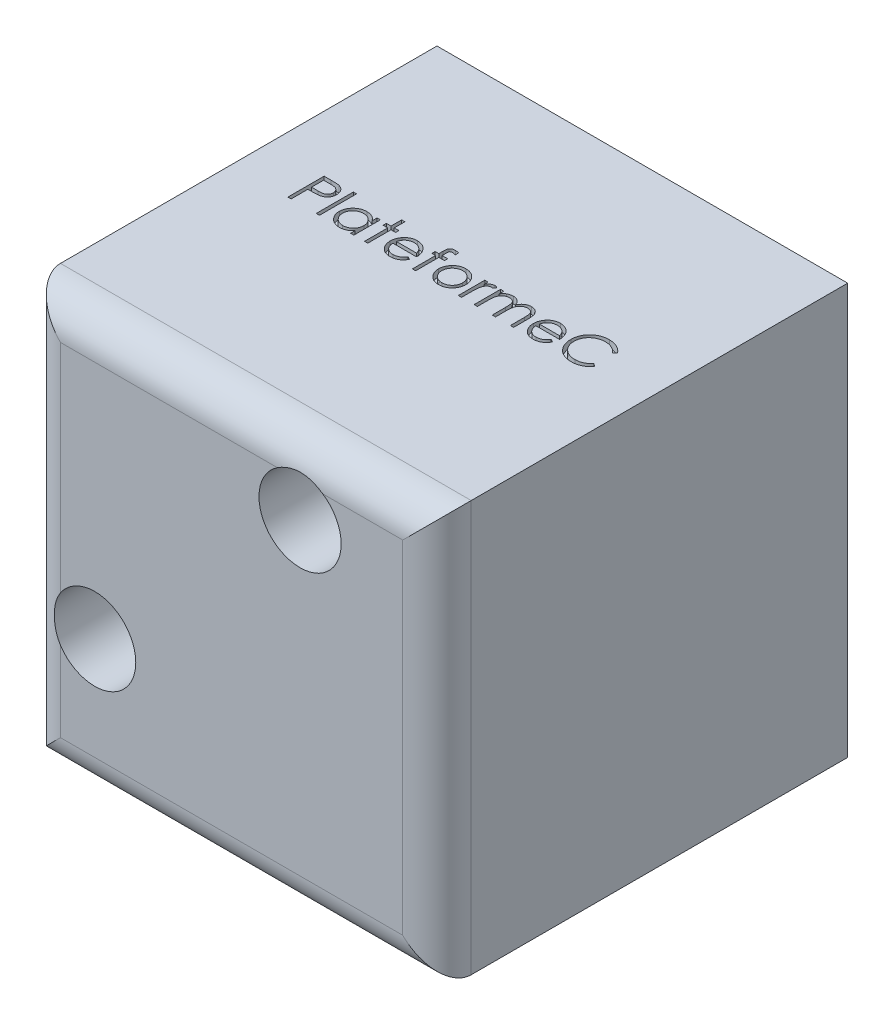
SolidWorks part; units mm, degrees
ref_plane "Plan de face" through (0, 0, 0) normal (0, 0, 1) x (1, 0, 0)
ref_plane "Plan de dessus" through (0, 0, 0) normal (0, 1, 0) x (1, 0, 0)
ref_plane "Plan de droite" through (0, 0, 0) normal (1, 0, 0) x (0, 0, -1)
sketch "Esquisse1" plane through (0, 0, 0) normal (0, 0, 1) x (1, 0, 0)
  line L1 (0, 0) -> (-60, 0)
  line L2 (0, 0) -> (0, 60)
  line L3 (0, 60) -> (-60, 60)
  line L4 (-60, 0) -> (-60, 60)
  dimension "D1" = 60
  dimension "D2" = 60
extrude "Boss.-Extru.1" add sketch "Esquisse1" along normal blind 60
sketch "Esquisse3" plane through (0, 0, 0) normal (0, 0, -1) x (-1, 0, 0)
  line L0 (60, 60) -> (60, 20)
  line L1 (60, 60) -> (60, 0) construction
  line L2 (60, 20) -> (58, 20)
  line L3 (58, 20) -> (58, 58)
  line L4 (58, 58) -> (20, 58)
  line L5 (20, 58) -> (20, 60)
  line L6 (0, 60) -> (60, 60) construction
  line L7 (20, 60) -> (60, 60)
  dimension "D1" = 40
  dimension "D2" = 40
  dimension "D3" = 2
  dimension "D4" = 2
extrude "Boss.-Extru.3" add sketch "Esquisse3" along normal blind 40
sketch "Esquisse6" plane through (-60, 0, 0) normal (-1, 0, 0) x (0, 0, 1)
  line L0 (30, 0) -> (30, 60) construction
  line L1 (60, 0) -> (0, 0) construction
  line L2 (60, 60) -> (-40, 60) construction
  text T0 "PING" font "Century Gothic" height in points 48
extrude "Enlèv. mat.-Extru.3" cut sketch "Esquisse6" against normal blind 1
sketch "Esquisse7" plane through (0, 60, 0) normal (0, 1, 0) x (1, 0, 0)
  line L0 (0, -30) -> (-60, -30) construction
  line L1 (0, -60) -> (0, 0) construction
  line L2 (-60, -60) -> (-60, 40) construction
  text T0 "PlateformeC" font "Century Gothic" height in points 20
extrude "Enlèv. mat.-Extru.4" cut sketch "Esquisse7" against normal blind 1
sketch "Esquisse8" plane through (-60, 0, 0) normal (-1, 0, 0) x (0, 0, 1)
  line L0 (-40, 20) -> (0, 60)
  line L1 (60, 60) -> (-40, 60) construction
  line L2 (0, 60) -> (-40, 60)
  line L3 (-40, 60) -> (-40, 20)
  dimension "D1" = 45
extrude "Enlèv. mat.-Extru.5" cut sketch "Esquisse8" against normal blind 2
sketch "Esquisse11" plane through (0, 60, 0) normal (0, 1, 0) x (1, 0, 0)
  line L0 (-20, 40) -> (-60, 0)
  line L1 (-60, 0) -> (-61.461, 41.461)
  line L2 (-61.461, 41.461) -> (-20, 40)
extrude "Enlèv. mat.-Extru.6" cut sketch "Esquisse11" against normal blind 2
fillet "Congé1" radius 5 4 edges at (-30, 0, 60) (0, 30, 60) (-60, 30, 60) (-30, 60, 60)
sketch "Esquisse13" plane through (0, 0, 60) normal (0, 0, 1) x (1, 0, 0)
  line L0 (-60, 60) -> (0, 60) construction
  line L1 (-60, 0) -> (-60, 60) construction
  circle A0 centre (-50, 20) radius 2.25
  circle A1 centre (-20, 50) radius 2.25
  dimension "D1" = 4.5
  dimension "D2" = 4.5
  dimension "D3" = 10
  dimension "D4" = 10
  dimension "D5" = 40
  dimension "D6" = 40
extrude "Enlèv. mat.-Extru.7" cut sketch "Esquisse13" against normal through all
sketch "Esquisse14" plane through (0, 0, 60) normal (0, 0, 1) x (1, 0, 0)
  circle A0 centre (-50, 20) radius 6
  circle A1 centre (-20, 50) radius 6
  dimension "D1" = 12
  dimension "D2" = 12
extrude "Enlèv. mat.-Extru.8" cut sketch "Esquisse14" against normal blind 54
sketch "Esquisse15" plane through (0, 0, 0) normal (0, -1, 0) x (1, 0, 0)
  line L1 (6.2592, -44.3072) -> (-60, -44.3072)
  line L2 (6.2592, -44.3072) -> (6.2592, 0)
  line L3 (6.2592, 0) -> (-60, 0)
  line L4 (-60, -44.3072) -> (-60, 0)
extrude "Enlèv. mat.-Extru.9" cut sketch "Esquisse15" against normal through all
